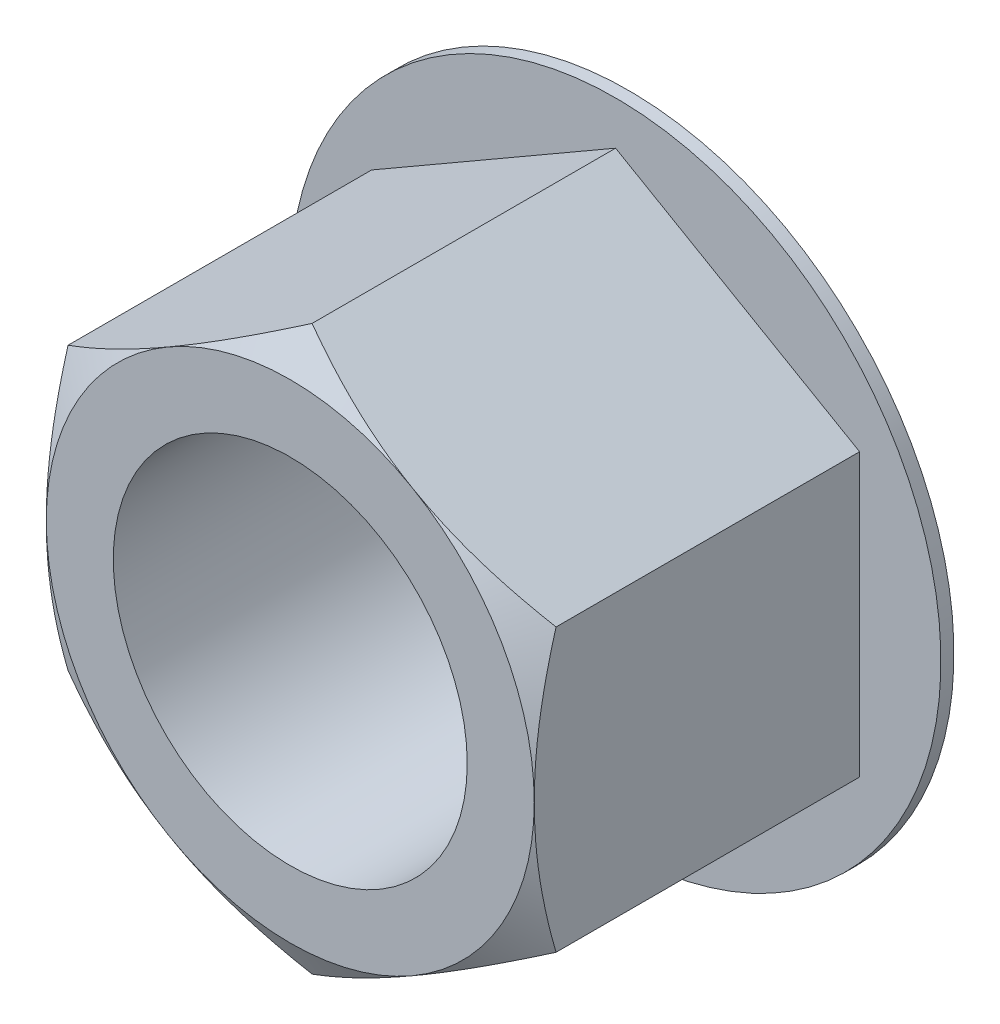
SolidWorks part; units mm, degrees
ref_plane "Front" through (0, 0, 0) normal (0, 0, 1) x (1, 0, 0)
ref_plane "Top" through (0, 0, 0) normal (0, 1, 0) x (1, 0, 0)
ref_plane "Right" through (0, 0, 0) normal (1, 0, 0) x (0, 0, -1)
sketch "Sketch1" plane through (0, 0, 0) normal (0, 0, 1) x (1, 0, 0)
  line L1 (4.7625, -2.7496) -> (4.7625, 2.7496)
  line L2 (4.7625, 2.7496) -> (0, 5.4993)
  line L3 (0, 5.4993) -> (-4.7625, 2.7496)
  line L4 (-4.7625, 2.7496) -> (-4.7625, -2.7496)
  line L5 (-4.7625, -2.7496) -> (0, -5.4993)
  line L6 (0, -5.4993) -> (4.7625, -2.7496)
  circle A0 centre (0, 0) radius 4.7625 construction
  dimension "Hex" = 9.525
extrude "Extrude1" add sketch "Sketch1" along normal mid plane 6.604
sketch "Sketch2" plane through (0, 0, 3.302) normal (0, 0, 1) x (1, 0, 0)
  circle A0 centre (0, 0) radius 4.7625 construction
  circle A5 centre (0, 0) radius 4.7625
extrude "Cut-Extrude1" cut sketch "Sketch2" against normal through all draft 60 flip side to cut
sketch "Sketch17" plane through (0, 0, -3.302) normal (0, 0, -1) x (-1, 0, 0)
  circle A0 centre (0, 0) radius 6.35
  dimension "Flange OD" = 12.7
extrude "Extrude3" add sketch "Sketch17" against normal blind 0.254
hole_wizard "5/16-24 Tapped Hole1" positions "Sketch19" profile "Sketch18" tap size "5/16-24" standard "ANSI Inch" end condition through all
sketch "Sketch19" plane through (0, 0, 3.302) normal (0, 0, 1) x (1, 0, 0)
  point P0 (0, 0)
cosmetic thread "Hole Thread1" parameters "D2"=7.9375
sketch "Sketch18" plane through (0, 0, 3.302) normal (1, 0, 0) x (0, -1, 0)
  line L0 (0, 0) -> (0, 6.604)
  line L1 (0, 6.604) -> (3.4544, 6.604)
  line L2 (3.4544, 6.604) -> (3.4544, 0)
  line L5 (3.4544, 0) -> (0, 0)
  line L11 (0, -6.35) -> (0, 107.95) construction
  dimension "Thru Tap Drill Dia." = 6.9088
  dimension "Thru Tap Drill Depth" = 6.604
move or copy body "Body-Move/Copy1" [suppressed] bodies to move or copy 115
